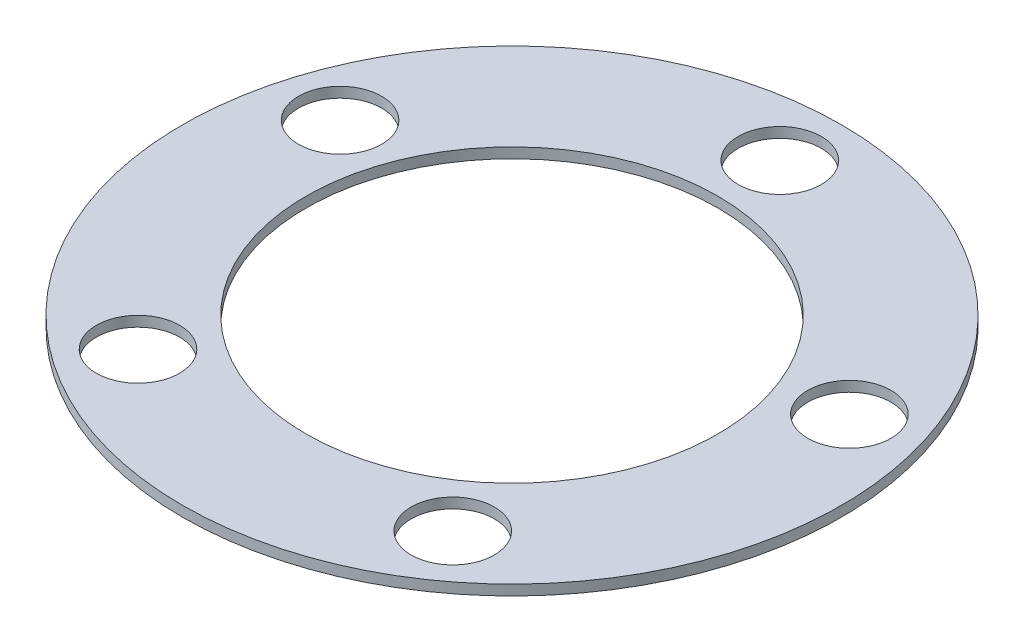
SolidWorks part; units mm, degrees
material "6061 Alloy"
ref_plane "Front Plane" through (0, 0, 0) normal (0, 0, 1) x (1, 0, 0)
ref_plane "Top Plane" through (0, 0, 0) normal (0, 1, 0) x (1, 0, 0)
ref_plane "Right Plane" through (0, 0, 0) normal (1, 0, 0) x (0, 0, -1)
sketch "Sketch1" plane through (0, 0, 0) normal (0, 1, 0) x (1, 0, 0)
  circle A0 centre (0, 0) radius 101.6
  dimension "D1" = 203.2
extrude "Boss-Extrude1" add sketch "Sketch1" along normal blind 3.175
sketch "Sketch2" plane through (0, 3.175, 0) normal (0, 1, 0) x (1, 0, 0)
  circle A0 centre (0, 82.55) radius 12.827
  circle A1 centre (78.5097, 25.5094) radius 12.827
  circle A2 centre (48.5217, -66.7844) radius 12.827
  circle A3 centre (-48.5217, -66.7844) radius 12.827
  circle A4 centre (-78.5097, 25.5094) radius 12.827
  point P12 (0, 0)
  dimension "D1" = 25.654
  dimension "D3" = 82.55
  dimension "D2" = 5
extrude "Cut-Extrude1" cut sketch "Sketch2" against normal blind 3.175
sketch "Sketch3" plane through (0, 3.175, 0) normal (0, 1, 0) x (1, 0, 0)
  circle A0 centre (0, 0) radius 63.5
  dimension "D1" = 127
extrude "Cut-Extrude2" cut sketch "Sketch3" against normal through all
